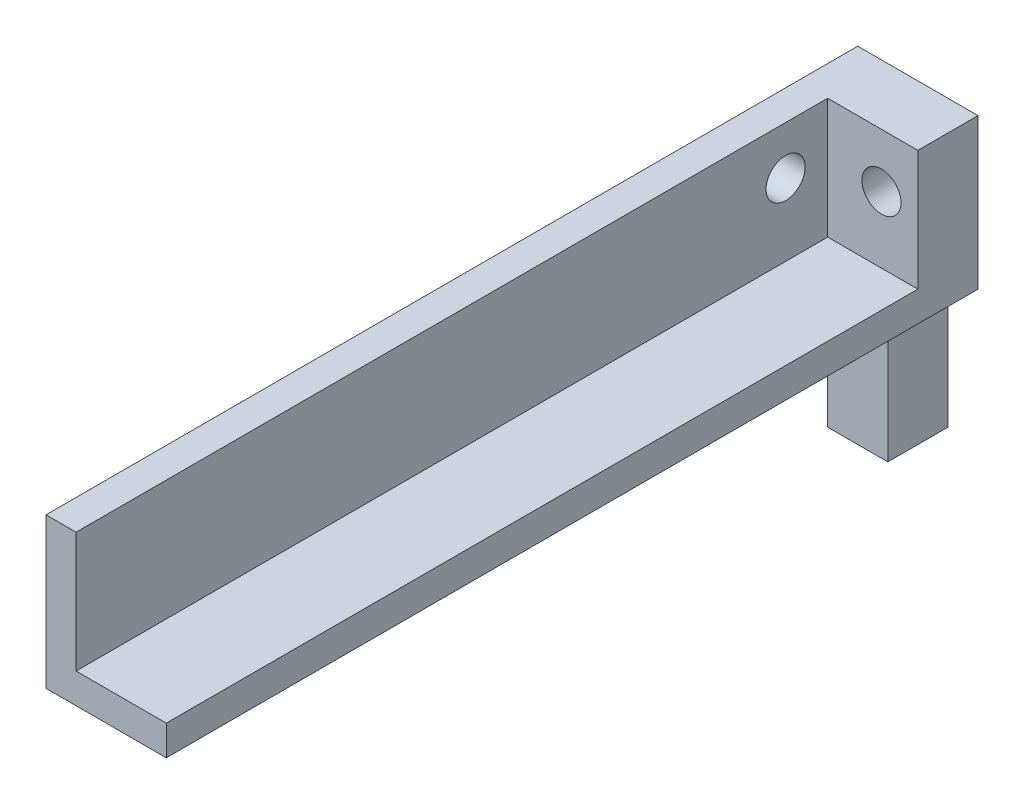
SolidWorks part; units mm, degrees
ref_plane "Front Plane" through (0, 0, 0) normal (0, 0, 1) x (1, 0, 0)
ref_plane "Top Plane" through (0, 0, 0) normal (0, 1, 0) x (1, 0, 0)
ref_plane "Right Plane" through (0, 0, 0) normal (1, 0, 0) x (0, 0, -1)
sketch "Sketch1" plane through (0, 0, 0) normal (1, 0, 0) x (0, 0, -1)
  line L0 (0, -1509.5556) -> (0, 73968.222) construction
  line L1 (0, 0) -> (-10, 0)
  line L2 (-10, 0) -> (-10, -20)
  line L3 (-10, -20) -> (-30, -20)
  line L6 (0, -47.38) -> (0, 0)
  line L7 (-30, -20) -> (-30, -25)
  line L8 (-30, -25) -> (-10, -25)
  line L9 (-10, -25) -> (-10, -47.38)
  line L10 (-10, -47.38) -> (0, -47.38)
  dimension "D1" = 20
  dimension "D2" = 20
  dimension "D3" = 5
  dimension "D4" = 10
  dimension "D5" = 10
  dimension "D6" = 22.38
extrude "Boss-Extrude1" add sketch "Sketch1" along normal blind 10
sketch "Sketch2" plane through (0, 0, 0) normal (-1, 0, 0) x (0, 0, 1)
  line L1 (0, 0) -> (30, 0)
  line L2 (0, 0) -> (0, -25)
  line L3 (0, -25) -> (30, -25)
  line L4 (30, 0) -> (30, -25)
extrude "Boss-Extrude2" add sketch "Sketch2" along normal blind 5
sketch "Sketch3" plane through (10, 0, 0) normal (1, 0, 0) x (0, 0, -1)
  line L0 (-10, 0) -> (-10, -20)
  line L1 (-10, -20) -> (-30, -20)
  line L2 (-30, -20) -> (-30, -25)
  line L3 (-30, -25) -> (-10, -25)
  line L4 (-10, -25) -> (0, -25)
  line L5 (0, -25) -> (0, 0)
  line L6 (0, 0) -> (-10, 0)
extrude "Boss-Extrude3" add sketch "Sketch3" along normal blind 5
sketch "Sketch4" plane through (0, 0, 30) normal (0, 0, 1) x (1, 0, 0)
  line L0 (-5, 0) -> (-5, -25)
  line L1 (-5, -25) -> (15, -25)
  line L2 (15, -25) -> (15, -20)
  line L3 (15, -20) -> (0, -20)
  line L4 (0, -20) -> (0, 0)
  line L5 (0, 0) -> (-5, 0)
extrude "Boss-Extrude4" add sketch "Sketch4" along normal up to surface (105 mm away)
sketch "Sketch7" plane through (0, 0, 0) normal (0, 0, -1) x (-1, 0, 0)
  circle A0 centre (-8.9559, -8.9641) radius 3.25
extrude "Cut-Extrude10" cut sketch "Sketch7" against normal blind 13 and the other way blind 15
sketch "Sketch8" plane through (-5, 0, 0) normal (-1, 0, 0) x (0, 0, 1)
  circle A0 centre (17, -8) radius 3.25
extrude "Cut-Extrude11" cut sketch "Sketch8" against normal blind 14 and the other way blind 17 contours A0
